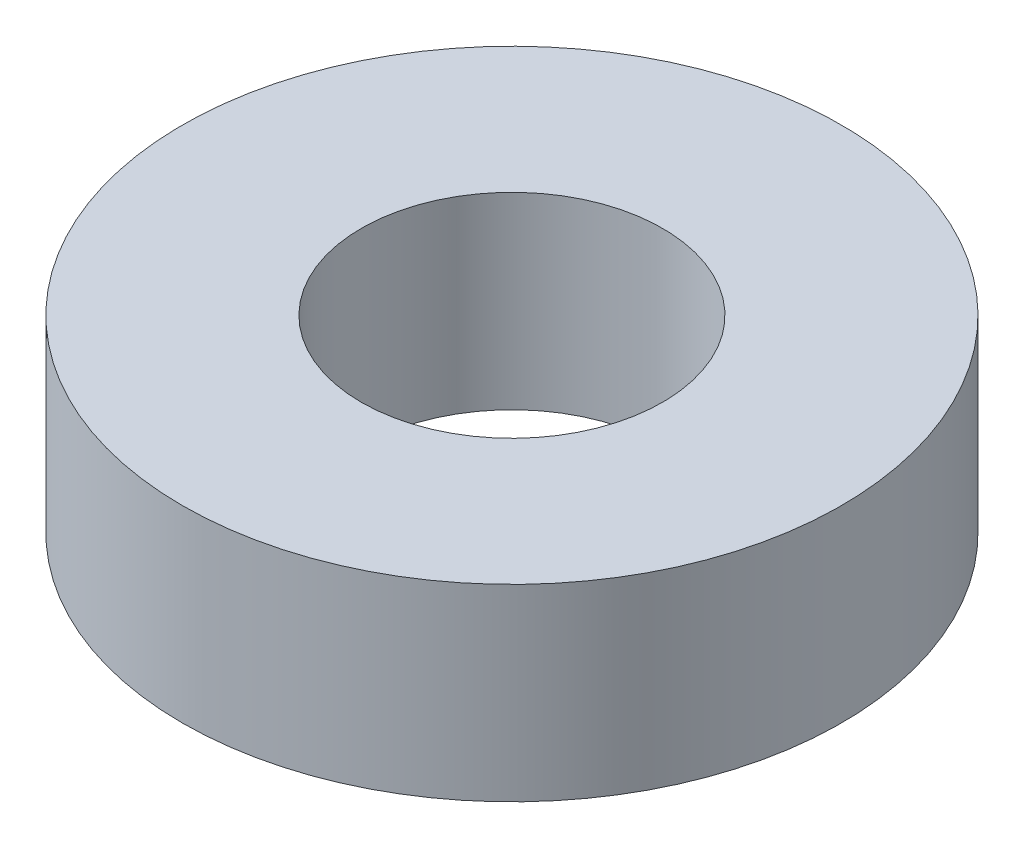
SolidWorks part; units mm, degrees
ref_plane "Alzado" through (0, 0, 0) normal (0, 0, 1) x (1, 0, 0)
ref_plane "Planta" through (0, 0, 0) normal (0, 1, 0) x (1, 0, 0)
ref_plane "Vista lateral" through (0, 0, 0) normal (1, 0, 0) x (0, 0, -1)
sketch "Sketch3" plane through (0, 0, 0) normal (0, 1, 0) x (1, 0, 0)
  circle A0 centre (0, 0) radius 1.6
  circle A1 centre (0, 0) radius 3.5
extrude "Boss-Extrude1" add sketch "Sketch3" along normal blind 2
